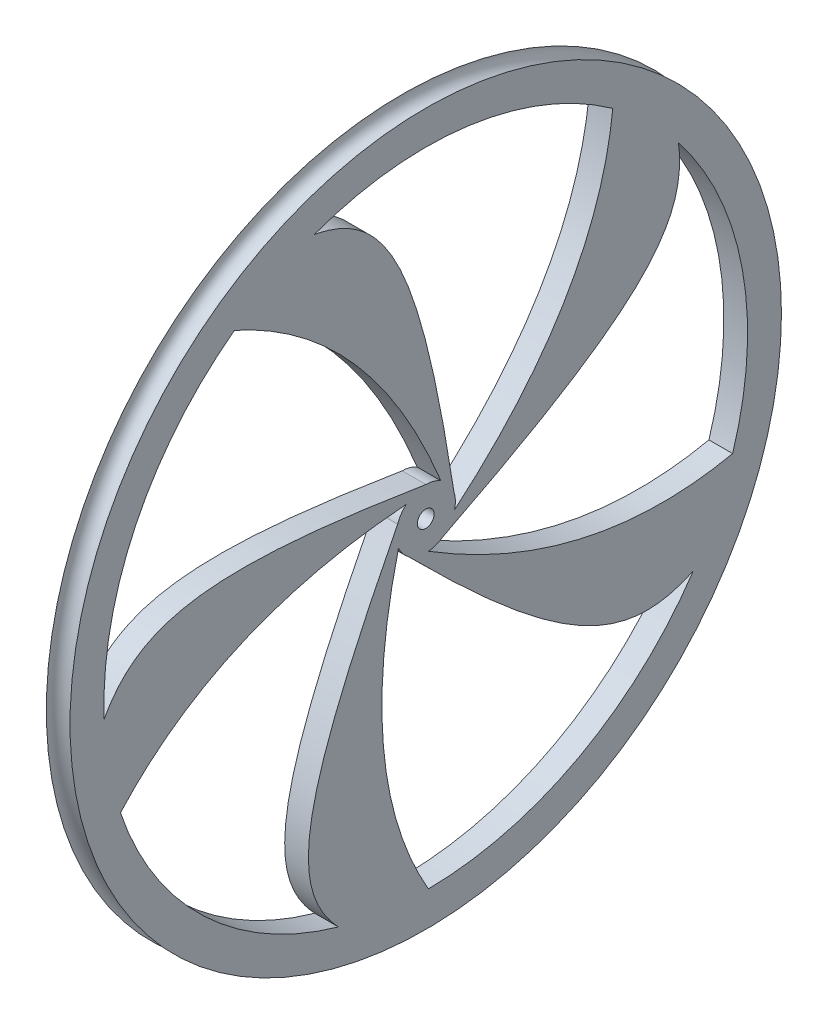
SolidWorks part; units mm, degrees
ref_plane "Front Plane" through (0, 0, 0) normal (0, 0, 1) x (1, 0, 0)
ref_plane "Top Plane" through (0, 0, 0) normal (0, 1, 0) x (1, 0, 0)
ref_plane "Right Plane" through (0, 0, 0) normal (1, 0, 0) x (0, 0, -1)
sketch "Sketch1" plane through (0, 0, 0) normal (0, 0, 1) x (1, 0, 0)
  line L0 (0, 0) -> (-8.3638, 0) construction
  line L1 (-1.778, 48.26) -> (1.778, 48.26)
  line L2 (-1.778, 48.26) -> (-1.778, 53.34)
  line L4 (1.778, 48.26) -> (1.778, 53.34)
  arc A0 (-1.778, 53.34) -> (1.778, 53.34) centre (0, 53.34) ccw
  point P7 (0, 48.26)
  dimension "D1" = 1.778
  dimension "D2" = 5.08
  dimension "D3" = 53.34
  dimension "D4" = 8.3638
revolve "Revolve1" add sketch "Sketch1" angle 360 about L0
sketch "Sketch3" plane through (0, 0, 0) normal (1, 0, 0) x (0, 0, -1)
  line L0 (1.0889, 0.6286) -> (-1.0889, 0.6286)
  circle A0 centre (0, 0) radius 1.2573
  circle A1 centre (0, 0) radius 4.445
  dimension "D1" = 2.5146
  dimension "D2" = 8.89
extrude "Boss-Extrude1" add sketch "Sketch3" along normal mid plane 3.556 separate body contours A1 A0
sketch "Sketch4" plane through (0, 0, 0) normal (1, 0, 0) x (0, 0, -1)
  line L0 (-4.445, 0) -> (4.445, 0) construction
  line L1 (-172.1158, 39.362) -> (67.2282, 47.9926) construction
  line L2 (-21.8469, 172.0075) -> (30.7369, -172.0075) construction
  circle A0 centre (0, 0) radius 48.26 construction
  circle A1 centre (0, 0) radius 48.26
  circle A2 centre (0, 0) radius 4.445 construction
  circle A3 centre (0, 0) radius 4.445
  circle A4 centre (0, 0) radius 68.2499 construction
  spline S0 degree 3 poles (4.445, 0) (-0.663, 33.4177) (-9.1182, 50.2135) (-35.803, 44.2774) (-52.4438, 43.6773) knots 0 0 0 0 0.582841 1 1 1 1
  spline S1 degree 2 poles (2.269, 3.8222) (-13.8361, 43.2073) (-52.4438, 43.6773) knots 0 0 0 1 1 1
  point P6 (-52.4438, 43.6773)
  point P14 (4.445, -0.0399)
  point P15 (-52.4438, 43.6773)
  dimension "D1" = 72.3398
  dimension "D2" = 136.4999
  dimension "D5" = 2.065
  dimension "D6" = 81.309
  dimension "D7" = 101.4175
  dimension "D8" = 49.9547
  dimension "D9" = 88.9045
  dimension "D3" = 3.8222
  dimension "D4" = 43.6773
extrude "Boss-Extrude2" add sketch "Sketch4" along normal mid plane 3.556 contours S1 A3 S0 A1
pattern_circular "CirPattern1" count 5 over 360 of "Boss-Extrude2"
